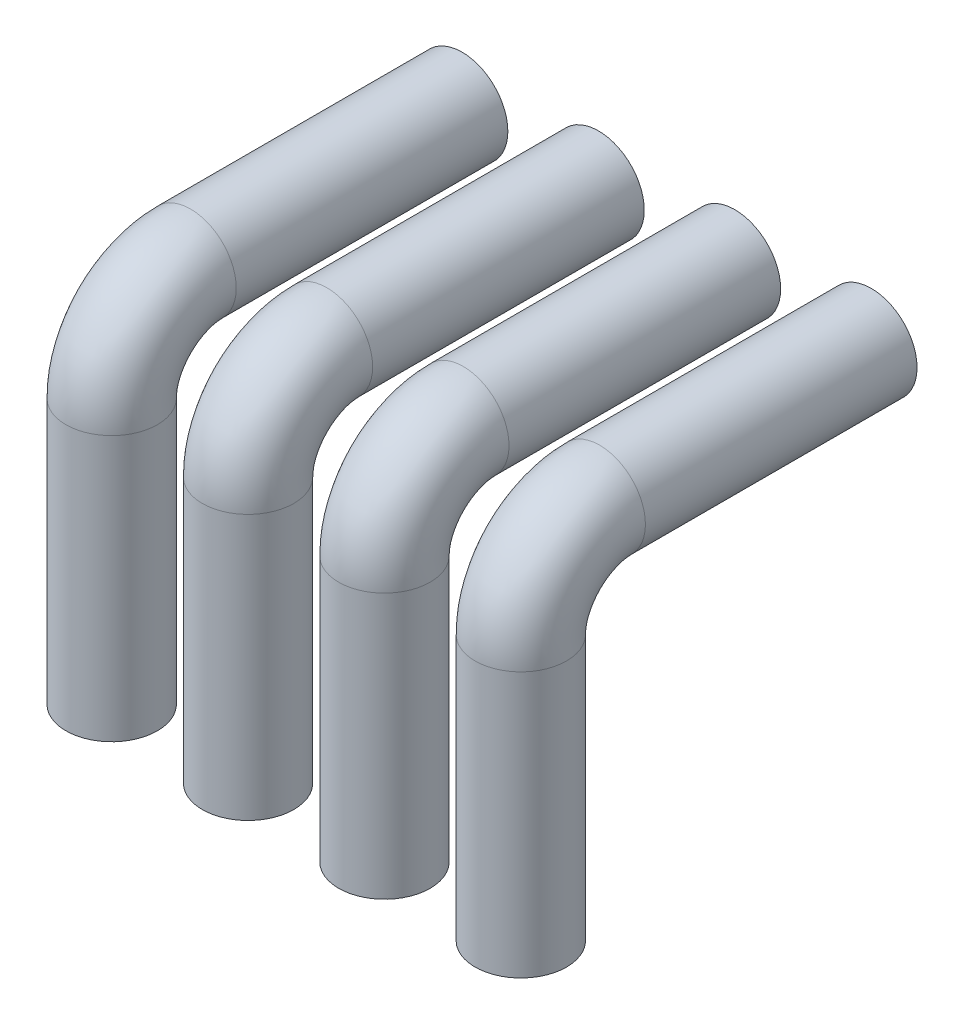
SolidWorks part; units mm, degrees
ref_plane "Front Plane" through (0, 0, 0) normal (0, 0, 1) x (1, 0, 0)
ref_plane "Top Plane" through (0, 0, 0) normal (0, 1, 0) x (1, 0, 0)
ref_plane "Right Plane" through (0, 0, 0) normal (1, 0, 0) x (0, 0, -1)
sketch "Sketch1" plane through (0, 0, 0) normal (0, 0, 1) x (1, 0, 0)
  circle A0 centre (0, 24.7351) radius 6.7083
  circle A1 centre (20, 24.7351) radius 6.7083
  circle A2 centre (40, 24.7351) radius 6.7083
  circle A3 centre (60, 24.7351) radius 6.7083
  dimension "D1" = 4
sketch "Sketch2" plane through (0, 0, 0) normal (1, 0, 0) x (0, 0, -1)
  line L0 (0, 24.7351) -> (-39.83, 24.7351)
  line L1 (-51.3893, 13.1757) -> (-51.3893, -25.7007)
  arc A0 (-39.83, 24.7351) -> (-51.3893, 13.1757) centre (-39.83, 13.1757) ccw
sweep "Sweep1" add profiles "Sketch1" path "Sketch2"
